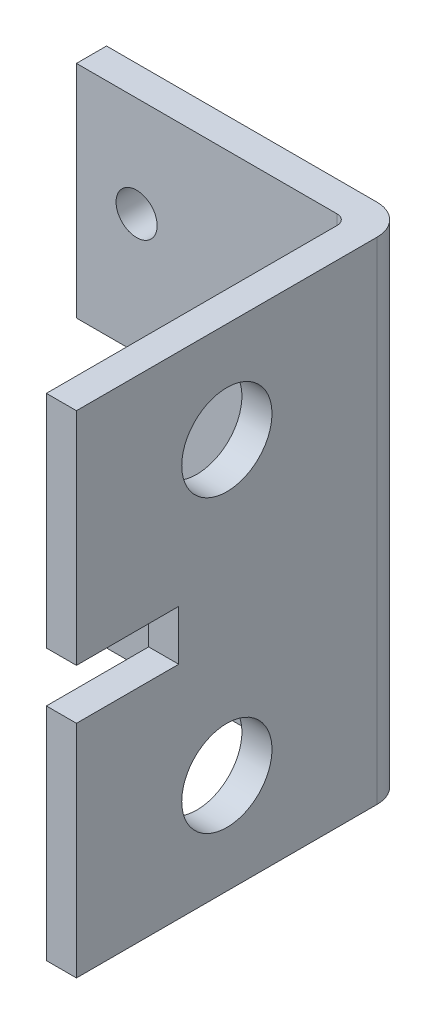
SolidWorks part; units mm, degrees
ref_plane "Front Plane" through (0, 0, 0) normal (0, 0, 1) x (1, 0, 0)
ref_plane "Top Plane" through (0, 0, 0) normal (0, 1, 0) x (1, 0, 0)
ref_plane "Right Plane" through (0, 0, 0) normal (1, 0, 0) x (0, 0, -1)
sketch "Sketch2" plane through (0, 0, 0) normal (0, 0, 1) x (1, 0, 0)
  line L1 (0, 0) -> (27, 0)
  line L2 (0, 0) -> (0, 49)
  line L3 (0, 49) -> (27, 49)
  line L4 (27, 0) -> (27, 49)
  line L5 (6, 39) -> (21, 39) construction
  line L6 (6, 39) -> (6, 10) construction
  line L7 (6, 10) -> (21, 10) construction
  line L8 (21, 39) -> (21, 10) construction
  circle A0 centre (6, 39) radius 2.05
  circle A1 centre (21, 39) radius 2.05
  circle A2 centre (6, 10) radius 2.05
  circle A3 centre (21, 10) radius 2.05
  point P13 (13.5, 10)
  point P14 (13.5, 0)
  point P15 (6, 24.5)
  point P16 (0, 24.5)
  dimension "D1" = 4.1
  dimension "D2" = 15
  dimension "D3" = 29
  dimension "D4" = 10
  dimension "D5" = 6
extrude "Boss-Extrude1" add sketch "Sketch2" along normal blind 3
sketch "Sketch4" plane through (0, 49, 0) normal (0, 1, 0) x (1, 0, 0)
  line L0 (27, 0) -> (0, 0) construction
  line L2 (30, -3) -> (30, -33)
  line L3 (30, -33) -> (27, -33)
  line L5 (27, -3) -> (27, 0) construction
  line L8 (27, -33) -> (27, 0)
  arc A0 (27, 0) -> (30, -3) centre (27, -3) cw
  dimension "D1" = 30
extrude "Boss-Extrude2" add sketch "Sketch4" against normal up to surface (49 mm away) up to face at (13.5, 0, 1.5)
sketch "Sketch5" plane through (27, 0, 0) normal (-1, 0, 0) x (0, 0, 1)
  line L1 (33, 0) -> (3, 0) construction
  line L2 (33, 0) -> (33, 49) construction
  circle A0 centre (18, 39) radius 4.5
  circle A1 centre (18, 10) radius 4.5
  dimension "D1" = 9
  dimension "D2" = 29
  dimension "D3" = 10
  dimension "D4" = 15
extrude "Cut-Extrude1" cut sketch "Sketch5" against normal through all
fillet "Fillet1" radius 1 1 edges at (27, 24.5, 3)
sketch "Sketch6" plane through (0, 0, 3) normal (0, 0, 1) x (1, 0, 0)
  line L0 (0, 49) -> (0, 0) construction
  line L1 (-3, 27) -> (10.2, 27)
  line L2 (-3, 27) -> (-3, 22)
  line L3 (-3, 22) -> (10.2, 22)
  line L4 (10.2, 27) -> (10.2, 22)
  point P8 (0, 24.5)
  point P9 (-3, 24.5)
  dimension "D1" = 5
  dimension "D2" = 3
  dimension "D3" = 10.2
extrude "Cut-Extrude2" cut sketch "Sketch6" against normal through all
sketch "Sketch7" plane through (27, 0, 0) normal (-1, 0, 0) x (0, 0, 1)
  line L0 (33, 0) -> (33, 49) construction
  line L1 (33, 27) -> (22.8, 27)
  line L2 (33, 27) -> (33, 22)
  line L3 (33, 22) -> (22.8, 22)
  line L4 (22.8, 27) -> (22.8, 22)
  line L5 (0, 27) -> (3, 27) construction
  line L6 (3, 22) -> (0, 22) construction
  dimension "D1" = 10.2
extrude "Cut-Extrude3" cut sketch "Sketch7" against normal through all and the other way through all
